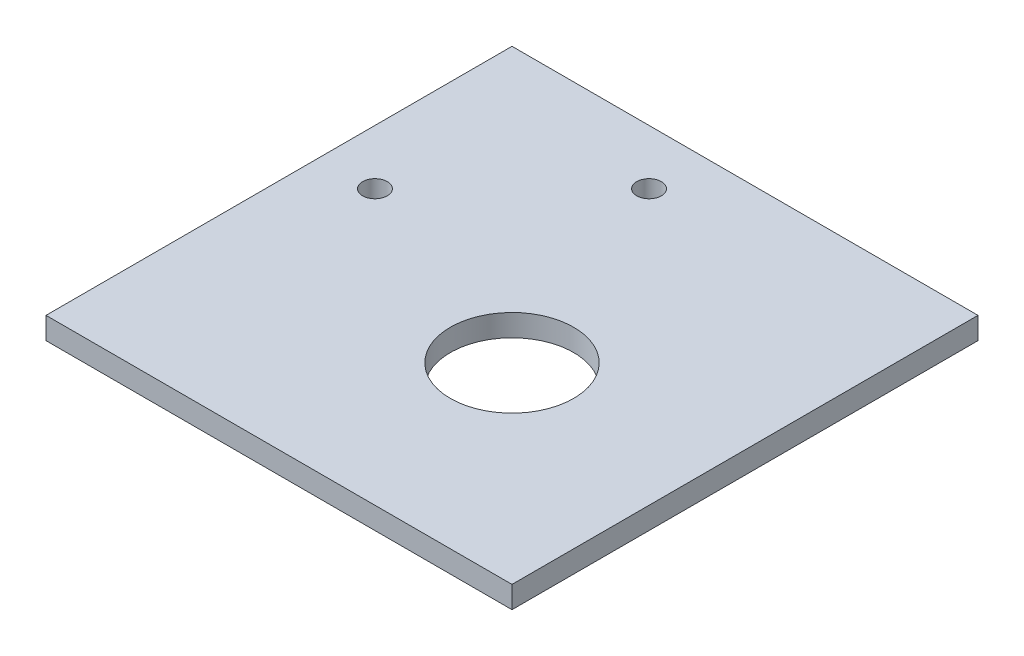
SolidWorks part; units mm, degrees
ref_plane "Front Plane" through (0, 0, 0) normal (0, 0, 1) x (1, 0, 0)
ref_plane "Top Plane" through (0, 0, 0) normal (0, 1, 0) x (1, 0, 0)
ref_plane "Right Plane" through (0, 0, 0) normal (1, 0, 0) x (0, 0, -1)
sketch "Sketch1" plane through (0, 0, 0) normal (0, 1, 0) x (1, 0, 0)
  line L1 (-50, 50) -> (35, 50)
  line L2 (-50, 50) -> (-50, -35)
  line L3 (-50, -35) -> (35, -35)
  line L4 (35, 50) -> (35, -35)
  circle A0 centre (0, 0) radius 11.25
  circle A1 centre (-15, 40) radius 2.25
  circle A2 centre (-40, 15) radius 2.25
  dimension "D1" = 22.5
  dimension "D6" = 35
  dimension "D8" = 4.5
  dimension "D9" = 50
  dimension "D10" = 50
  dimension "D2" = 85
  dimension "D3" = 85
  dimension "D4" = 35
  dimension "D5" = 10
  dimension "D7" = 10
extrude "Boss-Extrude1" add sketch "Sketch1" along normal blind 4
